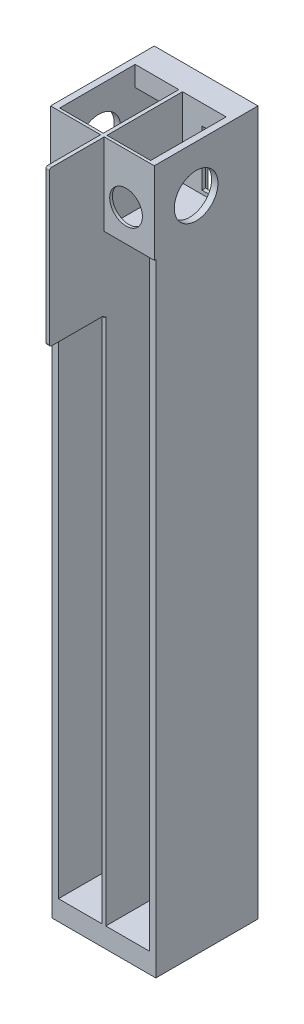
SolidWorks part; units mm, degrees
material "ABS"
ref_plane "Płaszczyzna przednia" through (0, 0, 0) normal (0, 0, 1) x (1, 0, 0)
ref_plane "Płaszczyzna górna" through (0, 0, 0) normal (0, 1, 0) x (1, 0, 0)
ref_plane "Płaszczyzna prawa" through (0, 0, 0) normal (1, 0, 0) x (0, 0, -1)
sketch "Szkic1" plane through (0, 0, 0) normal (0, 0, 1) x (1, 0, 0)
  line L0 (-90.4269, 49.2609) -> (-90.4269, -315.7391)
  line L1 (-91.9269, 53.7609) -> (-38.9269, 53.7609)
  line L2 (-91.9269, 53.7609) -> (-91.9269, -320.2391)
  line L3 (-91.9269, -320.2391) -> (-38.9269, -320.2391)
  line L4 (-38.9269, 53.7609) -> (-38.9269, -320.2391)
  line L5 (-40.4269, 49.2609) -> (-64.4269, 49.2609)
  line L6 (-90.4269, -315.7391) -> (-66.4269, -315.7391)
  line L7 (-90.4269, 49.2609) -> (-66.4269, 49.2609)
  line L8 (-66.4269, 49.2609) -> (-66.4269, -315.7391)
  line L10 (-64.4269, 49.2609) -> (-64.4269, -315.7391)
  line L13 (-40.4269, 49.2609) -> (-40.4269, -315.7391)
  line L14 (-40.4269, -315.7391) -> (-64.4269, -315.7391)
  dimension "D1" = 374
  dimension "D2" = 24
  dimension "D3" = 53
  dimension "D4" = 365
extrude "Dodanie-wyciągnięcie2" add sketch "Szkic1" along normal blind 12 contours L3 L4 L1 L2 | L6 L8 L7 L0 | L14 L10 L5 L13
sketch "Szkic2" plane through (-66.4269, 0, 0) normal (-1, 0, 0) x (0, 0, 1)
  line L0 (12, 49.2609) -> (12, -315.7391) construction
  line L1 (0, 49.2609) -> (12, 49.2609)
  line L2 (0, 49.2609) -> (0, 45.7609)
  line L3 (0, 45.7609) -> (12, 45.7609)
  line L4 (12, 49.2609) -> (12, 45.7609)
extrude "Wytnij-wyciągnięcie1" cut sketch "Szkic2" against normal blind 2
ref_plane "Płaszczyzna1" through (0, 0, 12) normal (0, 0, 1) x (1, 0, 0)
sketch "Szkic3" plane through (0, 0, 12) normal (0, 0, 1) x (1, 0, 0)
  line L6 (-38.9269, -320.2391) -> (-91.9269, -320.2391)
  line L7 (-38.9269, -320.2391) -> (-38.9269, 53.7609)
  line L8 (-38.9269, 53.7609) -> (-91.9269, 53.7609)
  line L9 (-91.9269, -320.2391) -> (-91.9269, 53.7609)
extrude "Dodanie-wyciągnięcie3" add sketch "Szkic3" along normal blind 2
sketch "Szkic4" plane through (0, 0, 14) normal (0, 0, 1) x (1, 0, 0)
  line L64 (-46.9269, -11.0391) -> (-56.3269, -11.0391)
  line L69 (-90.4269, 49.2609) -> (-40.4269, 49.2609) construction
  line L70 (-53.7269, 49.2609) -> (-40.4269, 49.2609)
  line L71 (-40.4269, 49.2609) -> (-40.4269, 18.7608)
  line L72 (-40.4269, 49.2609) -> (-40.4269, -315.7391) construction
  line L73 (-40.4269, 18.7608) -> (-53.7269, 18.7608)
  line L74 (-53.7269, 49.2609) -> (-53.7269, 18.7608)
  line L77 (-77.1269, 49.2609) -> (-77.1269, 18.7608)
  line L78 (-90.4269, 18.7608) -> (-77.1269, 18.7608)
  line L79 (-90.4269, 49.2609) -> (-90.4269, 18.7608)
  line L80 (-77.1269, 49.2609) -> (-90.4269, 49.2609)
  line L81 (-46.9269, -35.3991) -> (-46.9269, -40.4791)
  line L82 (-46.9269, -40.4791) -> (-56.3269, -40.4791)
  line L87 (-46.9269, -35.3991) -> (-46.9269, -11.0391)
  line L89 (-56.3269, -35.3991) -> (-56.3269, -11.0391)
  line L90 (-74.5269, -35.3991) -> (-74.5269, -11.0391)
  line L92 (-83.9269, -35.3991) -> (-83.9269, -11.0391)
  line L93 (-83.9269, -11.0391) -> (-74.5269, -11.0391)
  line L94 (-46.9269, -101.2391) -> (-46.9269, -166.1991)
  line L95 (-46.9269, -166.1991) -> (-56.3269, -166.1991)
  line L96 (-46.9269, -101.2391) -> (-56.3269, -101.2391)
  line L97 (-56.3269, -166.1991) -> (-56.3269, -101.2391)
  line L98 (-74.5269, -166.1991) -> (-74.5269, -101.2391)
  line L99 (-83.9269, -101.2391) -> (-74.5269, -101.2391)
  line L100 (-83.9269, -166.1991) -> (-74.5269, -166.1991)
  line L101 (-83.9269, -101.2391) -> (-83.9269, -166.1991)
  line L102 (-56.3269, -40.4791) -> (-56.3269, -35.3991)
  line L103 (-74.5269, -35.3991) -> (-74.5269, -40.4791)
  line L104 (-74.5269, -40.4791) -> (-83.9269, -40.4791)
  line L105 (-83.9269, -40.4791) -> (-83.9269, -35.3991)
extrude "Wytnij-wyciągnięcie2" cut sketch "Szkic4" against normal blind 2
sketch "Szkic5" plane through (0, 0, 14) normal (0, 0, 1) x (1, 0, 0)
  line L1 (-91.9269, -320.2391) -> (-38.9269, -320.2391) construction
  line L7 (-64.4269, -320.2391) -> (-66.4269, -320.2391)
  line L11 (-64.4269, -320.2391) -> (-64.4269, 53.7609)
  line L12 (-64.4269, 53.7609) -> (-66.4269, 53.7609)
  line L13 (-66.4269, -320.2391) -> (-66.4269, 53.7609)
extrude "Dodanie-wyciągnięcie4" add sketch "Szkic5" along normal blind 43
sketch "Szkic6" plane through (0, 0, 14) normal (0, 0, 1) x (1, 0, 0)
  line L0 (-64.4269, 16.7608) -> (-40.4269, 16.7608)
  line L4 (-64.4269, -320.2391) -> (-64.4269, 53.7609) construction
  line L5 (-40.4269, 49.2609) -> (-40.4269, -315.7391) construction
  line L6 (-40.4269, 16.7608) -> (-40.4269, 53.7609)
  line L7 (-91.9269, 53.7609) -> (-38.9269, 53.7609) construction
  line L8 (-40.4269, 53.7609) -> (-38.9269, 53.7609)
  line L19 (-90.4269, 53.7609) -> (-91.9269, 53.7609)
  line L20 (-90.4269, 16.7608) -> (-90.4269, 53.7609)
  line L21 (-66.4269, 16.7608) -> (-90.4269, 16.7608)
  line L22 (-64.4269, 16.7608) -> (-64.4269, 15.2608)
  line L23 (-64.4269, 15.2608) -> (-38.9269, 15.2608)
  line L24 (-38.9269, 15.2608) -> (-38.9269, 53.7609)
  line L25 (-91.9269, 15.2608) -> (-91.9269, 53.7609)
  line L26 (-66.4269, 15.2608) -> (-91.9269, 15.2608)
  line L27 (-66.4269, 16.7608) -> (-66.4269, 15.2608)
extrude "Dodanie-wyciągnięcie5" add sketch "Szkic6" along normal blind 41.5
ref_plane "Płaszczyzna2" through (0, 0, 55.5) normal (0, 0, 1) x (1, 0, 0)
sketch "Szkic7" plane through (0, 0, 55.5) normal (0, 0, 1) x (1, 0, 0)
  line L1 (-38.9269, 15.2608) -> (-64.4269, 15.2608)
  line L2 (-38.9269, 15.2608) -> (-38.9269, 53.7609)
  line L3 (-38.9269, 53.7609) -> (-64.4269, 53.7609)
  line L4 (-64.4269, 15.2608) -> (-64.4269, 53.7609)
  line L5 (-66.4269, 15.2608) -> (-91.9269, 15.2608)
  line L6 (-66.4269, 15.2608) -> (-66.4269, 53.7609)
  line L7 (-66.4269, 53.7609) -> (-91.9269, 53.7609)
  line L8 (-91.9269, 15.2608) -> (-91.9269, 53.7609)
extrude "Dodanie-wyciągnięcie6" add sketch "Szkic7" along normal blind 1.5
sketch "Szkic9" plane through (-91.9269, 0, 0) normal (-1, 0, 0) x (0, 0, 1)
  circle A1 centre (34, 34.5109) radius 12
extrude "Wytnij-wyciągnięcie4" cut sketch "Szkic9" against normal blind 1.5
sketch "Szkic10" plane through (0, 0, 14) normal (0, 0, 1) x (1, 0, 0)
  line L0 (-91.9269, 15.2608) -> (-91.9269, -320.2391)
  line L1 (-91.9269, -320.2391) -> (-66.4269, -320.2391)
  line L2 (-66.4269, -320.2391) -> (-66.4269, -315.7391)
  line L3 (-66.4269, 15.2608) -> (-66.4269, -320.2391) construction
  line L4 (-66.4269, -315.7391) -> (-90.4269, -315.7391)
  line L5 (-90.4269, -315.7391) -> (-90.4269, 15.2608)
  line L6 (-91.9269, 15.2608) -> (-66.4269, 15.2608) construction
  line L7 (-90.4269, 15.2608) -> (-91.9269, 15.2608)
  dimension "D1" = 330.9999
  dimension "D2" = 24
extrude "Dodanie-wyciągnięcie7" add sketch "Szkic10" along normal blind 43
sketch "Szkic11" plane through (0, 0, 14) normal (0, 0, 1) x (1, 0, 0)
  line L0 (-38.9269, 15.2608) -> (-38.9269, -320.2391)
  line L1 (-38.9269, -320.2391) -> (-64.4269, -320.2391)
  line L2 (-64.4269, -320.2391) -> (-64.4269, -315.7391)
  line L3 (-64.4269, -320.2391) -> (-64.4269, 15.2608) construction
  line L4 (-64.4269, -315.7391) -> (-40.4269, -315.7391)
  line L5 (-40.4269, -315.7391) -> (-40.4269, 15.2608)
  line L6 (-64.4269, 15.2608) -> (-38.9269, 15.2608) construction
  line L7 (-40.4269, 15.2608) -> (-38.9269, 15.2608)
  dimension "D1" = 330.9999
  dimension "D2" = 24
extrude "Dodanie-wyciągnięcie8" add sketch "Szkic11" along normal blind 43
sketch "Szkic12" plane through (-38.9269, 0, 0) normal (1, 0, 0) x (0, 0, -1)
  circle A0 centre (-34, 34.5109) radius 12
extrude "Wytnij-wyciągnięcie5" cut sketch "Szkic12" against normal blind 1.5
sketch "Szkic13" plane through (0, 0, 57) normal (0, 0, 1) x (1, 0, 0)
  circle A0 centre (-78.4269, 32.8109) radius 9
  circle A1 centre (-52.4269, 32.8109) radius 9
extrude "Wytnij-wyciągnięcie6" cut sketch "Szkic13" against normal blind 1.5
sketch "Szkic14" plane through (-38.9269, 0, 0) normal (1, 0, 0) x (0, 0, -1)
  line L1 (-57, -320.2391) -> (0, -320.2391)
  line L2 (-57, -320.2391) -> (-57, 53.7609)
  line L3 (-57, 53.7609) -> (0, 53.7609)
  line L4 (0, -320.2391) -> (0, 53.7609)
  circle A0 centre (-34, 34.5109) radius 12
extrude "Dodanie-wyciągnięcie9" add sketch "Szkic14" along normal blind 1
sketch "Szkic15" plane through (-91.9269, 0, 0) normal (-1, 0, 0) x (0, 0, 1)
  line L1 (57, 53.7609) -> (0, 53.7609)
  line L2 (57, 53.7609) -> (57, -320.2391)
  line L3 (57, -320.2391) -> (0, -320.2391)
  line L4 (0, 53.7609) -> (0, -320.2391)
  circle A0 centre (34, 34.5109) radius 12
extrude "Dodanie-wyciągnięcie10" add sketch "Szkic15" along normal blind 1
sketch "Szkic16" plane through (0, 53.7609, 0) normal (0, 1, 0) x (1, 0, 0)
  line L1 (-37.9269, -57) -> (-92.9269, -57)
  line L2 (-37.9269, -57) -> (-37.9269, 0)
  line L3 (-37.9269, 0) -> (-92.9269, 0)
  line L4 (-92.9269, -57) -> (-92.9269, 0)
  line L5 (-40.4269, -55.5) -> (-64.4269, -55.5)
  line L6 (-40.4269, -55.5) -> (-40.4269, -14)
  line L7 (-40.4269, -14) -> (-64.4269, -14)
  line L8 (-64.4269, -55.5) -> (-64.4269, -14)
  line L9 (-66.4269, -55.5) -> (-90.4269, -55.5)
  line L10 (-66.4269, -55.5) -> (-66.4269, -14)
  line L11 (-66.4269, -14) -> (-90.4269, -14)
  line L12 (-90.4269, -55.5) -> (-90.4269, -14)
extrude "Dodanie-wyciągnięcie11" add sketch "Szkic16" along normal blind 1
sketch "Szkic17" plane through (0, -320.2391, 0) normal (0, -1, 0) x (1, 0, 0)
  line L1 (-92.9269, 57) -> (-37.9269, 57)
  line L2 (-92.9269, 57) -> (-92.9269, 0)
  line L3 (-92.9269, 0) -> (-37.9269, 0)
  line L4 (-37.9269, 57) -> (-37.9269, 0)
extrude "Dodanie-wyciągnięcie12" add sketch "Szkic17" along normal blind 1
sketch "Szkic18" plane through (0, 0, 57) normal (0, 0, 1) x (1, 0, 0)
  line L0 (-64.4269, 15.2608) -> (-64.4269, 54.7609)
  line L2 (-66.4269, 15.2608) -> (-66.4269, 54.7609)
  line L3 (-66.4269, 54.7609) -> (-64.4269, 54.7609)
  line L4 (-66.4269, 15.2608) -> (-66.4269, -4.7392)
  line L5 (-66.4269, 15.2608) -> (-66.4269, -315.7391) construction
  line L7 (-64.4269, -315.7391) -> (-64.4269, 15.2608) construction
  line L8 (-64.4269, -4.7392) -> (-64.4269, 15.2608)
  line L9 (-66.4269, -4.7392) -> (-66.4269, -24.7392)
  line L10 (-66.4269, 15.2608) -> (-66.4269, -315.7391) construction
  line L11 (-66.4269, -24.7392) -> (-64.4269, -24.7392)
  line L12 (-64.4269, -315.7391) -> (-64.4269, 15.2608) construction
  line L13 (-64.4269, -24.7392) -> (-64.4269, -4.7392)
extrude "Dodanie-wyciągnięcie13" add sketch "Szkic18" along normal blind 30
sketch "Szkic20" plane through (0, -321.2391, 0) normal (0, -1, 0) x (1, 0, 0)
  line L1 (-92.9269, 57) -> (-37.9269, 57)
  line L2 (-92.9269, 57) -> (-92.9269, 0)
  line L3 (-92.9269, 0) -> (-37.9269, 0)
  line L4 (-37.9269, 57) -> (-37.9269, 0)
extrude "Dodanie-wyciągnięcie14" add sketch "Szkic20" along normal blind 5.5
sketch "Szkic21" plane through (0, 54.7609, 0) normal (0, 1, 0) x (1, 0, 0)
  line L0 (-64.4269, -87) -> (-66.4269, -87)
  line L1 (-66.4269, -87) -> (-66.4269, -57)
  line L2 (-66.4269, -57) -> (-92.9269, -57)
  line L3 (-92.9269, -57) -> (-92.9269, 0)
  line L4 (-92.9269, 0) -> (-37.9269, 0)
  line L5 (-37.9269, 0) -> (-37.9269, -57)
  line L6 (-37.9269, -57) -> (-64.4269, -57)
  line L7 (-64.4269, -57) -> (-64.4269, -87)
  line L9 (-40.4269, -55.5) -> (-64.4269, -55.5)
  line L10 (-40.4269, -55.5) -> (-40.4269, -14)
  line L11 (-40.4269, -14) -> (-64.4269, -14)
  line L12 (-64.4269, -55.5) -> (-64.4269, -14)
  line L13 (-66.4269, -55.5) -> (-90.4269, -55.5)
  line L14 (-66.4269, -55.5) -> (-66.4269, -14)
  line L15 (-66.4269, -14) -> (-90.4269, -14)
  line L16 (-90.4269, -55.5) -> (-90.4269, -14)
extrude "Dodanie-wyciągnięcie15" add sketch "Szkic21" along normal blind 5.5
sketch "Szkic22" plane through (-37.9269, 0, 0) normal (1, 0, 0) x (0, 0, -1)
  line L1 (-57, -326.7391) -> (0, -326.7391)
  line L2 (-57, -326.7391) -> (-57, 60.2609)
  line L3 (-57, 60.2609) -> (0, 60.2609)
  line L4 (0, -326.7391) -> (0, 60.2609)
  circle A0 centre (-34, 34.5109) radius 12
  dimension "D1" = 24
extrude "Dodanie-wyciągnięcie16" add sketch "Szkic22" along normal blind 1
sketch "Szkic23" plane through (-92.9269, 0, 0) normal (-1, 0, 0) x (0, 0, 1)
  line L1 (57, 60.2609) -> (0, 60.2609)
  line L2 (57, 60.2609) -> (57, -326.7391)
  line L3 (57, -326.7391) -> (0, -326.7391)
  line L4 (0, 60.2609) -> (0, -326.7391)
  circle A0 centre (34, 34.5109) radius 12
extrude "Dodanie-wyciągnięcie17" add sketch "Szkic23" along normal blind 1
fillet "Zaokrąglenie1" radius 1 1 edges at (-65.4269, -24.7392, 87)
fillet "Zaokrąglenie2" radius 1 1 edges at (-65.4269, -24.7392, 57)
fillet "Zaokrąglenie3" radius 1 1 edges at (-65.4269, 60.2609, 87)
sketch "Szkic24" plane through (0, 0, 57) normal (0, 0, 1) x (1, 0, 0)
  line L0 (-64.4269, 15.2608) -> (-64.4269, -25.7392)
  line L1 (-64.4269, -25.7392) -> (-66.4269, -25.7392)
  line L2 (-66.4269, -25.7392) -> (-66.4269, 15.2608)
  line L3 (-66.4269, 15.2608) -> (-93.9269, 15.2608)
  line L4 (-93.9269, -326.7391) -> (-93.9269, 60.2609) construction
  line L5 (-93.9269, 15.2608) -> (-93.9269, -326.7391)
  line L6 (-93.9269, -326.7391) -> (-36.9269, -326.7391)
  line L7 (-36.9269, -326.7391) -> (-36.9269, 15.2608)
  line L8 (-36.9269, 60.2609) -> (-36.9269, -326.7391) construction
  line L9 (-36.9269, 15.2608) -> (-64.4269, 15.2608)
extrude "Wytnij-wyciągnięcie7" cut sketch "Szkic24" against normal blind 0.85
